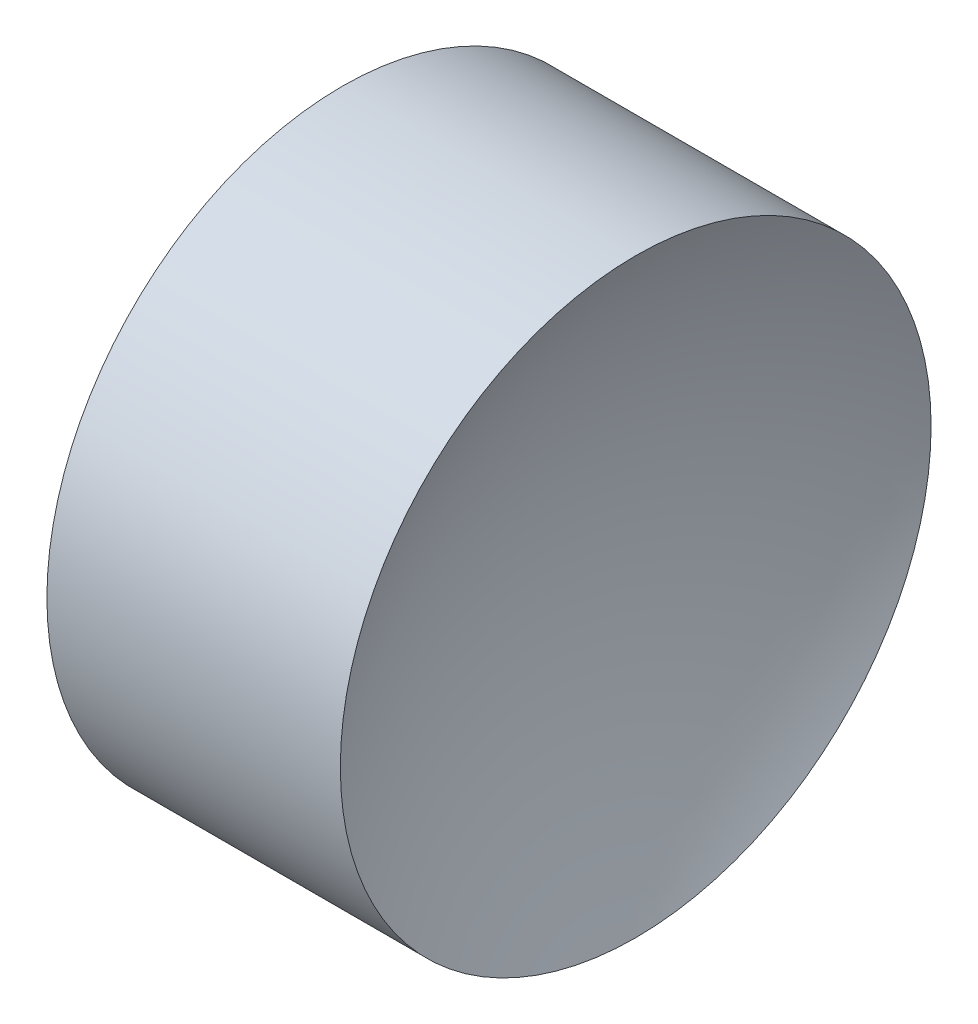
SolidWorks part; units mm, degrees
ref_plane "前视基准面" through (0, 0, 0) normal (0, 0, 1) x (1, 0, 0)
ref_plane "上视基准面" through (0, 0, 0) normal (0, 1, 0) x (1, 0, 0)
ref_plane "右视基准面" through (0, 0, 0) normal (1, 0, 0) x (0, 0, -1)
sketch "草图1" plane through (0, 0, 0) normal (0, 0, 1) x (1, 0, 0)
  line L0 (10.6125, 6.5223) -> (13.9161, 6.5223) construction
  line L1 (11.5149, 6.5223) -> (12.5149, 6.5223)
  line L3 (12.0149, 8.5223) -> (13.0083, 8.5223)
  line L4 (12.0149, 8.5223) -> (11.0215, 8.5223)
  arc A0 (13.0083, 8.5223) -> (12.5149, 6.5223) centre (16.8149, 6.5223) ccw
  arc A1 (11.5149, 6.5223) -> (11.0215, 8.5223) centre (7.2149, 6.5223) ccw
  dimension "D1" = 4.3
  dimension "D2" = 4.3
  dimension "D3" = 1.9869
revolve "旋转1" add sketch "草图1" angle 360 about L0
